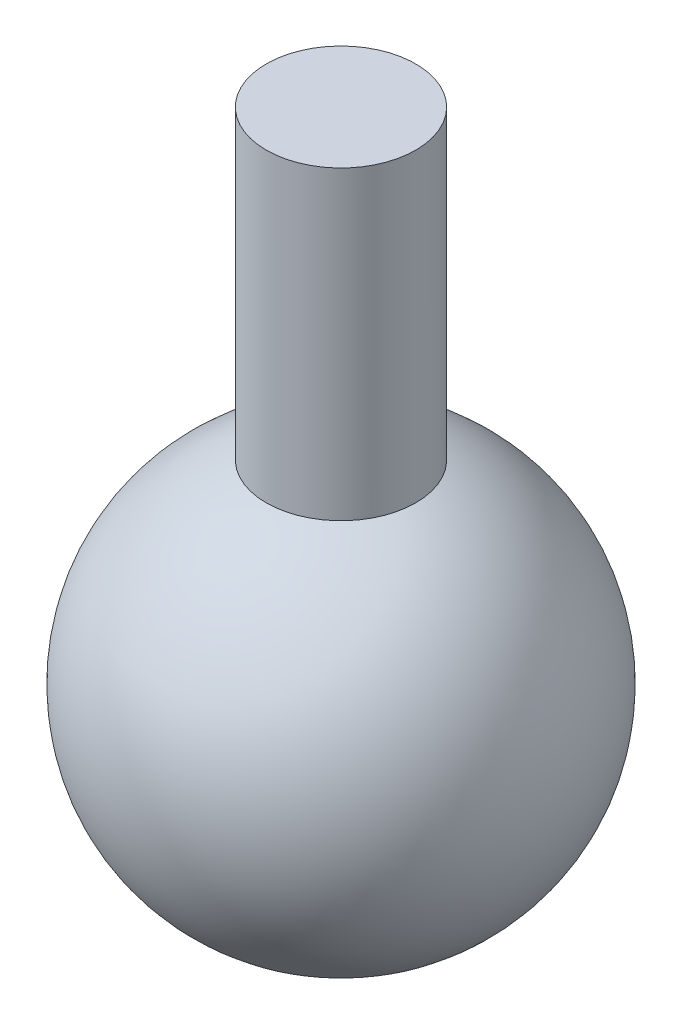
SolidWorks part; units mm, degrees
ref_plane "Front" through (0, 0, 0) normal (0, 0, 1) x (1, 0, 0)
ref_plane "Top" through (0, 0, 0) normal (0, 1, 0) x (1, 0, 0)
ref_plane "Right" through (0, 0, 0) normal (1, 0, 0) x (0, 0, -1)
sketch "Sketch1" plane through (0, 0, 0) normal (0, 0, 1) x (1, 0, 0)
  line L0 (0, 0) -> (0, -12.0271) construction
  line L1 (0, 28.8807) -> (0, -12.0271)
  line L2 (0, 28.8807) -> (4.3192, 28.8807)
  line L3 (4.3192, 11.2248) -> (4.3192, 28.8807)
  line L5 (0, 0) -> (11.2937, 4.1355) construction
  arc A0 (0, -12.0271) -> (4.3192, 11.2248) centre (0, 0) ccw
revolve "Revolve1" add sketch "Sketch1" angle 360 about L1
